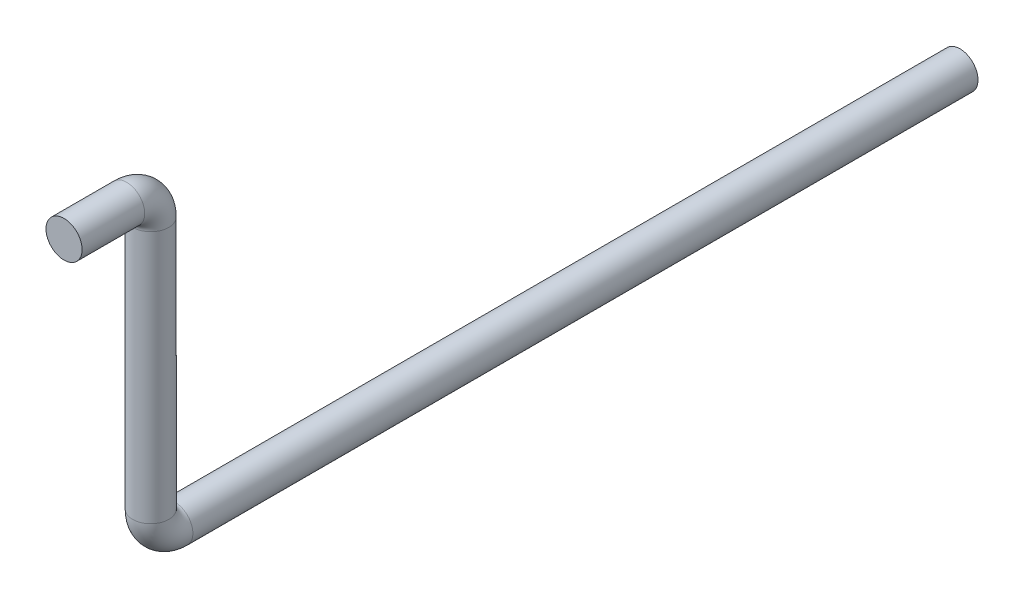
SolidWorks part; units mm, degrees
ref_plane "Alzado" through (0, 0, 0) normal (0, 0, 1) x (1, 0, 0)
ref_plane "Planta" through (0, 0, 0) normal (0, 1, 0) x (1, 0, 0)
ref_plane "Vista lateral" through (0, 0, 0) normal (1, 0, 0) x (0, 0, -1)
sketch "Croquis1" plane through (0, 0, 0) normal (0, 0, 1) x (1, 0, 0)
  circle A0 centre (4.6938, 15.1515) radius 7.5
  dimension "D1" = 15
sketch3d "Croquis3D1"
  line L0 (4.6938, 15.1515, 0) -> (4.6938, 15.1515, 26)
  line L1 (4.6938, 25.1515, 36) -> (4.6938, 130.1515, 36)
  line L2 (4.6938, 140.1515, 46) -> (4.6938, 140.1515, 72)
  arc A0 (4.6938, 15.1515, 26) -> (4.6938, 25.1515, 36) centre (4.6938, 25.1515, 26) ccw
  arc A1 (4.6938, 130.1515, 36) -> (4.6938, 140.1515, 46) centre (4.6938, 130.1515, 46) ccw
  point P7 (4.6938, 15.1515, 36)
  point P8 (-5.3062, 25.1515, 26)
  point P11 (4.6938, 140.1515, 36)
  point P12 (14.6938, 130.1515, 46)
  dimension "D4" = 10
  dimension "D1" = 36
  dimension "D2" = 36
  dimension "D3" = 125
sweep "Barrer1" add profiles "Croquis1" path "Croquis3D1"
sketch "Croquis2" plane through (0, 0, 0) normal (0, 0, -1) x (-1, 0, 0)
  circle A0 centre (-4.6938, 15.1515) radius 7.5
extrude "Saliente-Extruir1" add sketch "Croquis2" along normal blind 300
